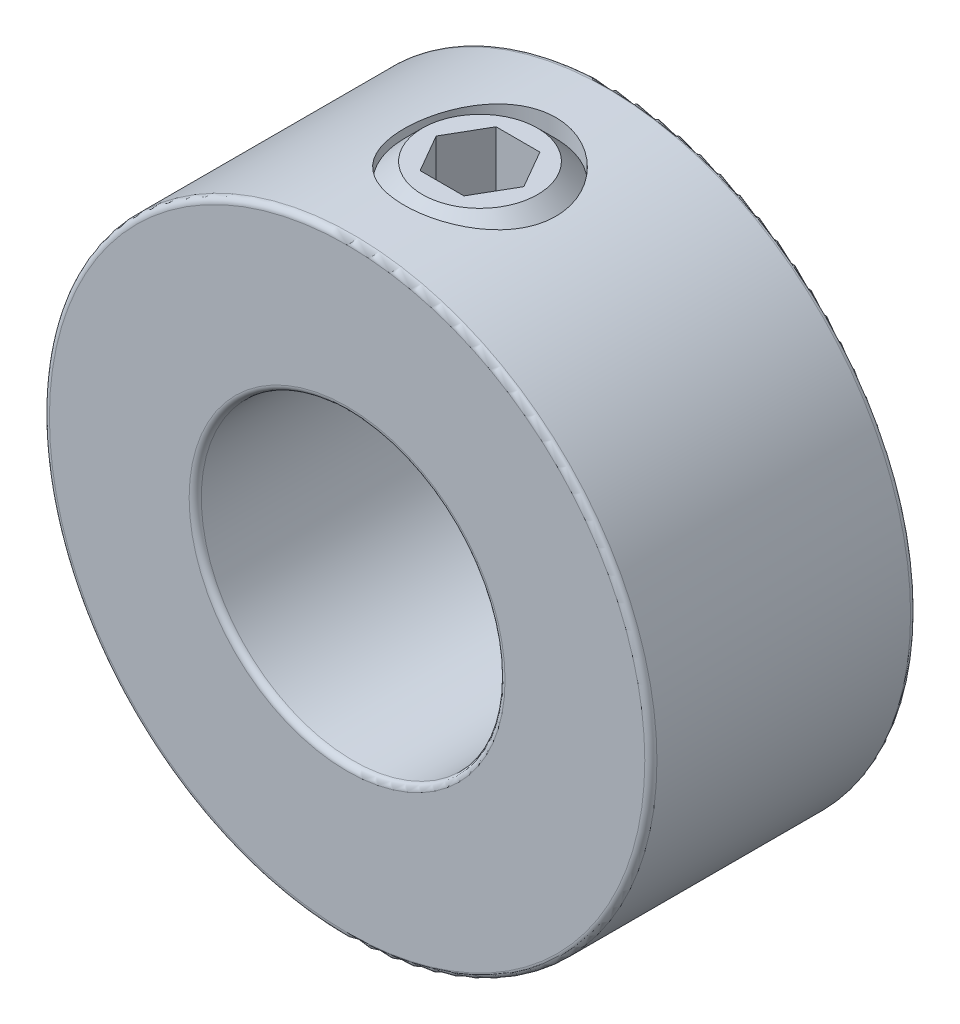
SolidWorks part; units mm, degrees
ref_plane "Front Plane" through (0, 0, 0) normal (0, 0, 1) x (1, 0, 0)
ref_plane "Top Plane" through (0, 0, 0) normal (0, 1, 0) x (1, 0, 0)
ref_plane "Right Plane" through (0, 0, 0) normal (1, 0, 0) x (0, 0, -1)
sketch "Sketch1" plane through (0, 0, 0) normal (0, 0, 1) x (1, 0, 0)
  circle A0 centre (0, 0) radius 12.7
  circle A1 centre (0, 0) radius 6.35
  point P4 (12.7, 0)
  dimension "Bore Dia" = 12.7
  dimension "OD" = 25.4
extrude "Extrude1" add sketch "Sketch1" along normal mid plane 11.1125
sketch "Sketch2" plane through (41.275, 0, 0) normal (0, -1, 0) x (0, 0, -1)
  line L0 (5.5562, -41.275) -> (-5.5563, -41.275) construction
  line L1 (-5.5562, -28.575) -> (-5.5562, -53.975) construction
  line L2 (5.5562, -53.975) -> (5.5562, -28.575) construction
  circle A0 centre (0, -41.275) radius 3.175
  point P7 (0, -44.45)
  dimension "Set Screw Dia" = 6.35
extrude "Cut-Extrude1" cut sketch "Sketch2" against normal through all
fillet "Fillet1" radius 0.254 4 edges at (6.35, 0, -5.5562) (6.35, 0, 5.5562) (12.7, 0, -5.5562) (12.7, 0, 5.5562)
sketch "Sketch3" plane through (0, 0, 0) normal (0, 0, 1) x (1, 0, 0)
  line L0 (-2.4082, 6.35) -> (-0.9202, 6.35)
  line L1 (0, 7.2702) -> (-0.9202, 6.35)
  line L2 (0, 7.2702) -> (0, 12.7)
  line L3 (0, 12.7) -> (-2.4082, 12.7)
  line L4 (-3.175, 7.1168) -> (-3.175, 11.9332)
  line L5 (0, 6.35) -> (0, 0) construction
  line L6 (-3.175, 7.1168) -> (-3.175, 6.35) construction
  line L7 (-3.175, 6.35) -> (-2.4082, 6.35) construction
  line L8 (-3.175, 11.9332) -> (-3.175, 12.7) construction
  line L9 (-2.4082, 6.35) -> (-3.175, 7.1168)
  line L10 (-3.175, 11.9332) -> (-2.4082, 12.7)
  line L11 (-3.175, 12.7) -> (-2.4082, 12.7) construction
  line L12 (-0.9202, 6.35) -> (0, 6.35) construction
  line L13 (0, 6.35) -> (0, 7.2702) construction
  circle A1 centre (0, 0) radius 6.35 construction
  dimension "Screw Length" = 6.35
  dimension "D2" = 0.7668
  dimension "D1" = 0.9202
revolve "Revolve1" add sketch "Sketch3" angle 360 about L5
sketch "Sketch4" plane through (3.3734, 12.7, 0) normal (0, -1, 0) x (0, 0, -1)
  line L1 (0, -1.5404) -> (-1.5875, -2.4569)
  line L2 (-1.5875, -2.4569) -> (-1.5875, -4.29)
  line L3 (-1.5875, -4.29) -> (0, -5.2065)
  line L4 (0, -5.2065) -> (1.5875, -4.29)
  line L5 (1.5875, -4.29) -> (1.5875, -2.4569)
  line L6 (1.5875, -2.4569) -> (0, -1.5404)
  circle A0 centre (0, -3.3734) radius 1.5875 construction
  circle A1 centre (0, -3.3734) radius 1.8331 construction
  dimension "D1" = 3.6662
  dimension "Hex Size" = 3.175
extrude "Cut-Extrude2" cut sketch "Sketch4" along normal blind 3.175
equation "\"D1@Fillet1\" = \"OD@Sketch1\"*.01"
equation "\"D1@Cut-Extrude2\" = \"Hex Size@Sketch4\""
equation "\"D2@Sketch3\" =(\"Set Screw Dia@Sketch2\"-\"D1@Sketch4\")/3.5"
equation "\"D1@Sketch3\" = \"D2@Sketch3\"*1.2"
